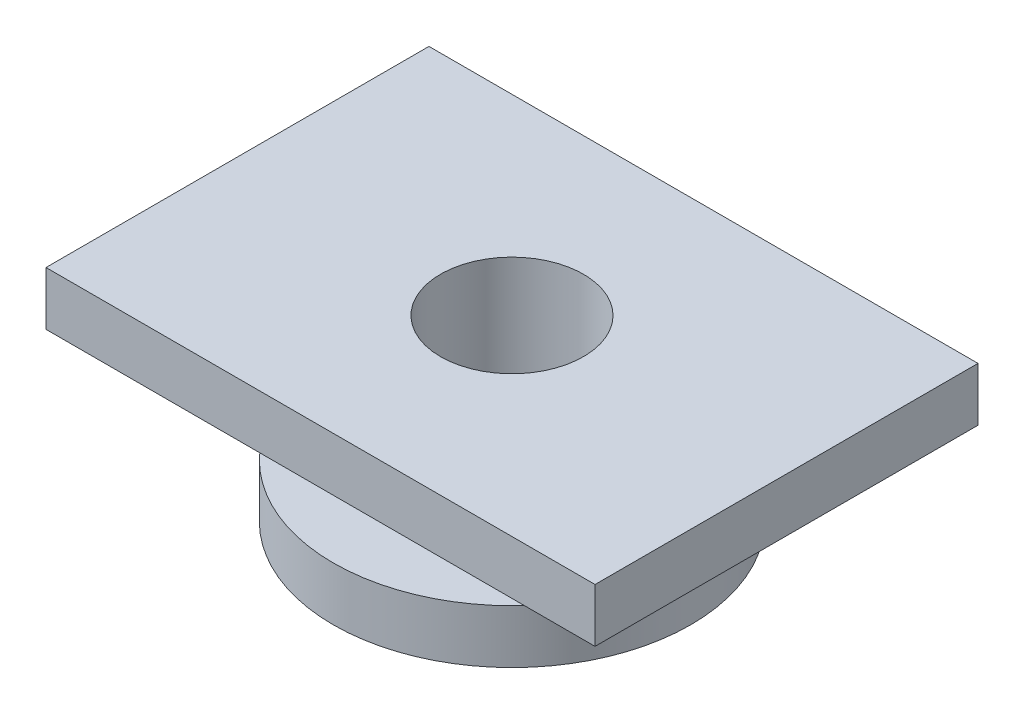
SolidWorks part; units mm, degrees
ref_plane "Front Plane" through (0, 0, 0) normal (0, 0, 1) x (1, 0, 0)
ref_plane "Top Plane" through (0, 0, 0) normal (0, 1, 0) x (1, 0, 0)
ref_plane "Right Plane" through (0, 0, 0) normal (1, 0, 0) x (0, 0, -1)
sketch "Sketch1" plane through (0, 0, 0) normal (0, 1, 0) x (1, 0, 0)
  circle A0 centre (0, 0) radius 4
  circle A1 centre (0, 0) radius 10
  dimension "D1" = 8
  dimension "D2" = 20
extrude "Boss-Extrude1" add sketch "Sketch1" along normal mid plane 3
sketch "Sketch2" plane through (0, 1.5, 0) normal (0, 1, 0) x (1, 0, 0)
  circle A0 centre (0, 0) radius 4
  circle A1 centre (0, 0) radius 6
  dimension "D1" = 8
  dimension "D2" = 2
extrude "Boss-Extrude2" add sketch "Sketch2" along normal blind 4
sketch "Sketch3" plane through (0, 5.5, 0) normal (0, 1, 0) x (1, 0, 0)
  line L1 (-15.3654, 10.7178) -> (15.3654, 10.7178)
  line L2 (-15.3654, 10.7178) -> (-15.3654, -10.7178)
  line L3 (-15.3654, -10.7178) -> (15.3654, -10.7178)
  line L4 (15.3654, 10.7178) -> (15.3654, -10.7178)
  line L5 (-15.3654, 10.7178) -> (15.3654, -10.7178) construction
  line L6 (-15.3654, -10.7178) -> (15.3654, 10.7178) construction
  circle A0 centre (0, 0) radius 4
  point P0 (0, 0)
  dimension "D3" = 8
  dimension "D1" = 21.4355
  dimension "D2" = 30.7308
extrude "Boss-Extrude3" add sketch "Sketch3" along normal blind 3
